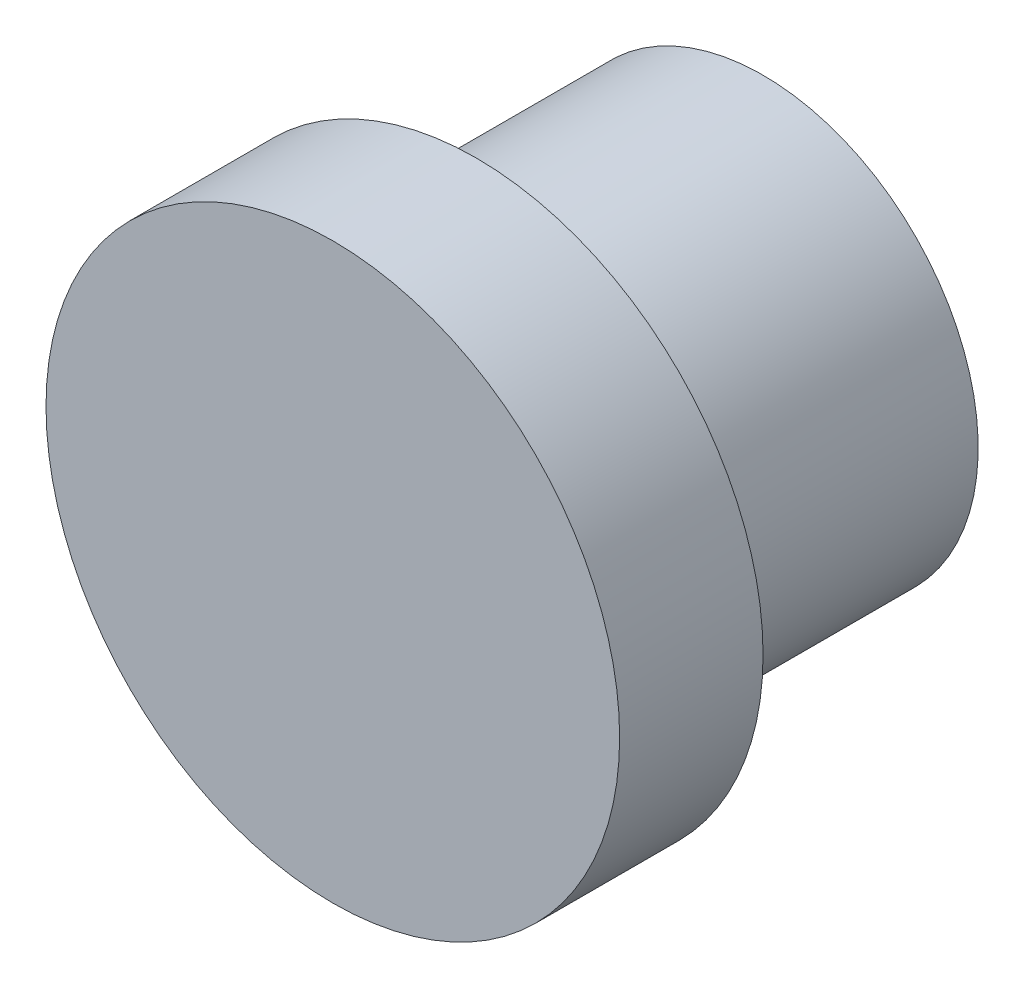
SolidWorks part; units mm, degrees
ref_plane "Спереди" through (0, 0, 0) normal (0, 0, 1) x (1, 0, 0)
ref_plane "Сверху" through (0, 0, 0) normal (0, 1, 0) x (1, 0, 0)
ref_plane "Справа" through (0, 0, 0) normal (1, 0, 0) x (0, 0, -1)
sketch "Эскиз1" plane through (0, 0, 0) normal (0, 0, 1) x (1, 0, 0)
  circle A0 centre (0, 0) radius 8
  dimension "D1" = 16
extrude "Бобышка-Вытянуть1" add sketch "Эскиз1" along normal blind 12
sketch "Эскиз2" plane through (0, 0, 0) normal (0, 0, -1) x (-1, 0, 0)
  circle A0 centre (0, 0) radius 6
  dimension "D1" = 12
extrude "Вырез-Вытянуть1" cut sketch "Эскиз2" against normal blind 8 flip side to cut
